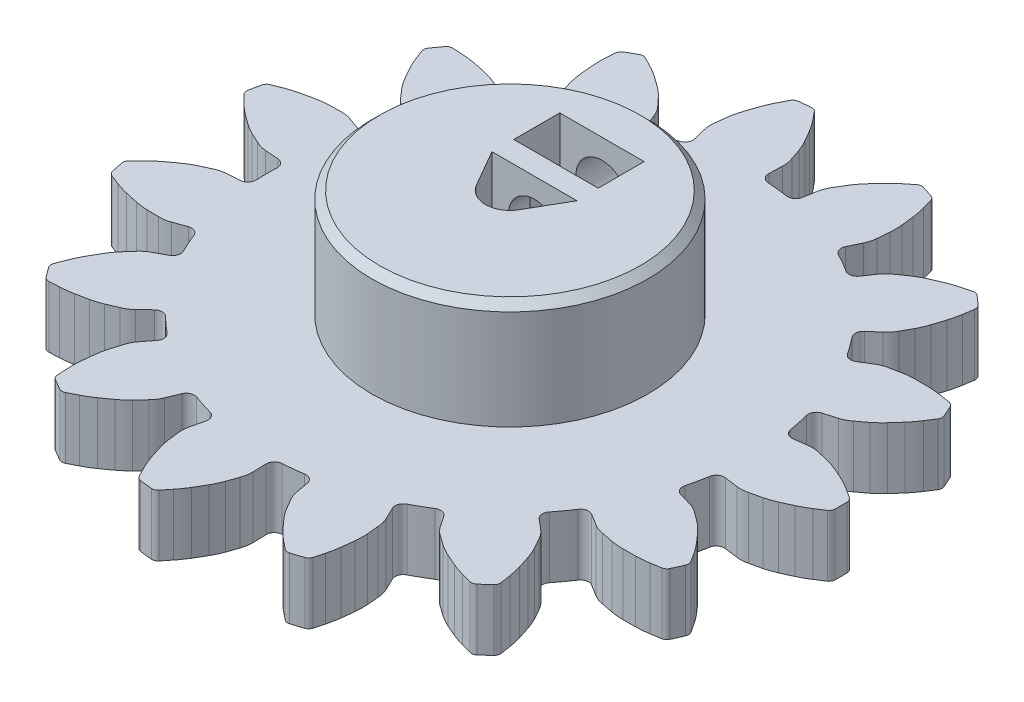
SolidWorks part; units mm, degrees
ref_plane "Front Plane" through (0, 0, 0) normal (0, 0, 1) x (1, 0, 0)
ref_plane "Top Plane" through (0, 0, 0) normal (0, 1, 0) x (1, 0, 0)
ref_plane "Right Plane" through (0, 0, 0) normal (1, 0, 0) x (0, 0, -1)
sketch "Sketch1" plane through (0, 0, 0) normal (0, 1, 0) x (1, 0, 0)
  line L0 (625.6555, 307.002) -> (626.5156, 307.1185)
  line L1 (625.6555, 302.598) -> (626.5156, 302.4815)
  line L2 (625.1464, 300.2026) -> (625.9795, 299.9593)
  line L3 (623.3551, 296.1794) -> (624.0934, 295.7232)
  line L4 (621.9157, 294.1982) -> (622.5778, 293.6371)
  line L5 (618.643, 291.2514) -> (619.1318, 290.5343)
  line L6 (616.5221, 290.027) -> (616.8987, 289.245)
  line L7 (612.3337, 288.6661) -> (612.4887, 287.8121)
  line L8 (609.8982, 288.4101) -> (609.9242, 287.5426)
  line L9 (605.5184, 288.8704) -> (605.3126, 288.0273)
  line L10 (603.1894, 289.6272) -> (602.8603, 288.8241)
  line L11 (599.3755, 291.8292) -> (598.8445, 291.1426)
  line L12 (597.5556, 293.4678) -> (596.9283, 292.868)
  line L13 (594.967, 297.0306) -> (594.2027, 296.6194)
  line L14 (593.9709, 299.2679) -> (593.1539, 298.975)
  line L15 (593.0553, 303.5755) -> (592.1898, 303.5107)
  line L16 (593.0553, 306.0245) -> (592.1898, 306.0893)
  line L17 (593.9709, 310.3321) -> (593.1539, 310.625)
  line L18 (594.967, 312.5694) -> (594.2027, 312.9806)
  line L19 (597.5556, 316.1322) -> (596.9283, 316.732)
  line L20 (599.3755, 317.7708) -> (598.8445, 318.4574)
  line L21 (603.1894, 319.9728) -> (602.8603, 320.7759)
  line L22 (605.5184, 320.7296) -> (605.3126, 321.5727)
  line L23 (609.8982, 321.1899) -> (609.9242, 322.0574)
  line L24 (612.3337, 320.9339) -> (612.4887, 321.7879)
  line L25 (616.5221, 319.573) -> (616.8987, 320.355)
  line L26 (618.643, 318.3486) -> (619.1318, 319.0657)
  line L27 (621.9157, 315.4018) -> (622.5778, 315.9629)
  line L28 (623.3551, 313.4206) -> (624.0934, 313.8768)
  line L29 (625.1464, 309.3974) -> (625.9795, 309.6407)
  line L30 (593.5318, 304.8) -> (630.9968, 304.8) construction
  line L31 (607.15, 326.2717) -> (611.0662, 289.012) construction
  arc A0 (625.0608, 307.4397) -> (624.9349, 308.1006) centre (609.4068, 304.8) ccw
  arc A1 (627.2484, 307.0745) -> (626.5156, 307.1185) centre (626.7704, 305.238) ccw
  arc A2 (627.9948, 306.9048) -> (627.2484, 307.0745) centre (97.3308, -2025.8777) ccw
  arc A3 (628.7466, 306.6443) -> (627.9948, 306.9048) centre (626.7164, 302.0004) ccw
  arc A4 (629.499, 306.3037) -> (628.7466, 306.6443) centre (616.4504, 278.4846) ccw
  arc A5 (630.2476, 305.8885) -> (629.499, 306.3037) centre (626.7956, 300.5468) ccw
  arc A6 (630.8146, 305.5178) -> (630.2476, 305.8885) centre (599.5148, 258.2574) ccw
  arc A7 (630.9968, 304.8) -> (630.9932, 305.1924) centre (609.4068, 304.8) ccw
  arc A8 (630.9932, 305.1924) -> (630.8146, 305.5178) centre (630.5943, 305.1852) ccw
  arc A9 (625.0608, 307.4397) -> (625.6555, 307.002) centre (625.5843, 307.528) ccw
  arc A10 (624.9349, 301.4994) -> (625.0608, 302.1603) centre (609.4068, 304.8) ccw
  arc A11 (626.5156, 302.4815) -> (627.2484, 302.5255) centre (626.7704, 304.362) ccw
  arc A12 (627.2484, 302.5255) -> (627.9948, 302.6952) centre (97.3308, 2635.4777) ccw
  arc A13 (627.9948, 302.6952) -> (628.7466, 302.9557) centre (626.7164, 307.5996) ccw
  arc A14 (628.7466, 302.9557) -> (629.499, 303.2963) centre (616.4504, 331.1154) ccw
  arc A15 (629.499, 303.2963) -> (630.2476, 303.7115) centre (626.7956, 309.0532) ccw
  arc A16 (630.2476, 303.7115) -> (630.8146, 304.0822) centre (599.5148, 351.3426) ccw
  arc A17 (630.9932, 304.4076) -> (630.9968, 304.8) centre (609.4068, 304.8) ccw
  arc A18 (630.8146, 304.0822) -> (630.9932, 304.4076) centre (630.5943, 304.4148) ccw
  arc A19 (625.6555, 302.598) -> (625.0608, 302.1603) centre (625.5843, 302.072) ccw
  arc A20 (624.7811, 300.8445) -> (624.9349, 301.4994) centre (609.4068, 304.8) ccw
  arc A21 (626.631, 299.621) -> (625.9795, 299.9593) centre (625.4473, 298.1377) ccw
  arc A22 (627.2439, 299.1624) -> (626.631, 299.621) centre (-806.37, -1616.1) ccw
  arc A23 (627.8248, 298.6186) -> (627.2439, 299.1624) centre (624.0812, 295.202) ccw
  arc A24 (628.3735, 298.0014) -> (627.8248, 298.6186) centre (605.138, 277.8948) ccw
  arc A25 (628.8885, 297.3177) -> (628.3735, 298.0014) centre (623.5623, 293.8419) ccw
  arc A26 (629.2558, 296.7484) -> (628.8885, 297.3177) centre (581.4394, 266.3046) ccw
  arc A27 (629.1302, 296.0186) -> (629.2866, 296.3785) centre (609.4068, 304.8) ccw
  arc A28 (629.2866, 296.3785) -> (629.2558, 296.7484) centre (628.9192, 296.5341) ccw
  arc A29 (624.7811, 300.8445) -> (625.1464, 300.2026) centre (625.2952, 300.7122) ccw
  arc A30 (622.2499, 295.4689) -> (622.6337, 296.0214) centre (609.4068, 304.8) ccw
  arc A31 (624.0934, 295.7232) -> (624.7808, 295.4653) centre (625.0911, 297.3375) ccw
  arc A32 (624.7808, 295.4653) -> (625.5316, 295.3167) centre (1089.5741, 2642.2601) ccw
  arc A33 (625.5316, 295.3167) -> (626.3245, 295.2489) centre (626.3586, 300.3171) ccw
  arc A34 (626.3245, 295.2489) -> (627.1503, 295.2541) centre (626.5449, 325.9754) ccw
  arc A35 (627.1503, 295.2541) -> (628.0031, 295.3289) centre (627.0222, 301.6128) ccw
  arc A36 (628.0031, 295.3289) -> (628.6718, 295.4369) centre (619.3006, 351.3423) ccw
  arc A37 (628.9674, 295.6615) -> (629.1302, 296.0186) centre (609.4068, 304.8) ccw
  arc A38 (628.6718, 295.4369) -> (628.9674, 295.6615) centre (628.6059, 295.8304) ccw
  arc A39 (623.3551, 296.1794) -> (622.6337, 296.0214) centre (623.0761, 295.7279) ccw
  arc A40 (621.8431, 294.9331) -> (622.2499, 295.4689) centre (609.4068, 304.8) ccw
  arc A41 (623.0354, 293.0631) -> (622.5778, 293.6371) centre (621.3508, 292.1894) ccw
  arc A42 (623.4088, 292.3948) -> (623.0354, 293.0631) centre (-1465.27, -874.1812) ccw
  arc A43 (623.7183, 291.6618) -> (623.4088, 292.3948) centre (618.9087, 290.0631) ccw
  arc A44 (623.9685, 290.8747) -> (623.7183, 291.6618) centre (594.5637, 281.9572) ccw
  arc A45 (624.1609, 290.0406) -> (623.9685, 290.8747) centre (617.8814, 289.0317) ccw
  arc A46 (624.2649, 289.3712) -> (624.1609, 290.0406) centre (568.1998, 281.0081) ccw
  arc A47 (623.8533, 288.7555) -> (624.1426, 289.0207) centre (609.4068, 304.8) ccw
  arc A48 (624.1426, 289.0207) -> (624.2649, 289.3712) centre (623.8702, 289.3123) ccw
  arc A49 (621.8431, 294.9331) -> (621.9157, 294.1982) centre (622.2589, 294.6032) ccw
  arc A50 (617.3443, 291.0518) -> (617.9196, 291.4005) centre (609.4068, 304.8) ccw
  arc A51 (619.1318, 290.5343) -> (619.6548, 290.0192) centre (620.6998, 291.6033) ccw
  arc A52 (619.6548, 290.0192) -> (620.2804, 289.578) centre (1998.7922, 2244.8744) ccw
  arc A53 (620.2804, 289.578) -> (620.9771, 289.1936) centre (623.0697, 293.8098) ccw
  arc A54 (620.9771, 289.1936) -> (621.7337, 288.8624) centre (633.676, 317.174) ccw
  arc A55 (621.7337, 288.8624) -> (622.5431, 288.5839) centre (624.2029, 294.7236) ccw
  arc A56 (622.5431, 288.5839) -> (623.198, 288.4106) centre (637.3756, 343.2943) ccw
  arc A57 (623.5593, 288.4956) -> (623.8533, 288.7555) centre (609.4068, 304.8) ccw
  arc A58 (623.198, 288.4106) -> (623.5593, 288.4956) centre (623.2978, 288.7969) ccw
  arc A59 (618.643, 291.2514) -> (617.9196, 291.4005) centre (618.2043, 290.9524) ccw
  arc A60 (616.7547, 290.7279) -> (617.3443, 291.0518) centre (609.4068, 304.8) ccw
  arc A61 (617.0833, 288.5345) -> (616.8987, 289.245) centre (615.189, 288.4216) ccw
  arc A62 (617.1526, 287.7722) -> (617.0833, 288.5345) centre (-1765.4397, 71.5942) ccw
  arc A63 (617.1372, 286.9766) -> (617.1526, 287.7722) centre (612.0932, 287.4725) ccw
  arc A64 (617.0457, 286.1558) -> (617.1372, 286.9766) centre (586.556, 289.9693) ccw
  arc A65 (616.8822, 285.3156) -> (617.0457, 286.1558) centre (610.7352, 286.948) ccw
  arc A66 (616.7049, 284.6618) -> (616.8822, 285.3156) centre (562.0853, 299.8254) ccw
  arc A67 (616.0785, 284.2667) -> (616.4506, 284.3913) centre (609.4068, 304.8) ccw
  arc A68 (616.4506, 284.3913) -> (616.7049, 284.6618) centre (616.3204, 284.7685) ccw
  arc A69 (616.7547, 290.7279) -> (616.5221, 290.027) centre (617.0004, 290.2573) ccw
  arc A70 (611.0662, 289.012) -> (611.7336, 289.0964) centre (609.4068, 304.8) ccw
  arc A71 (612.4887, 287.8121) -> (612.757, 287.1288) centre (614.3559, 288.1509) ccw
  arc A72 (612.757, 287.1288) -> (613.149, 286.4713) centre (2667.7729, 1512.0322) ccw
  arc A73 (613.149, 286.4713) -> (613.6291, 285.8368) centre (617.4184, 289.2027) ccw
  arc A74 (613.6291, 285.8368) -> (614.1855, 285.2265) centre (636.6108, 306.2331) ccw
  arc A75 (614.1855, 285.2265) -> (614.8117, 284.6429) centre (618.8253, 289.5766) ccw
  arc A76 (614.8117, 284.6429) -> (615.3395, 284.2181) centre (650.6147, 328.5903) ccw
  arc A77 (615.7042, 284.1488) -> (616.0785, 284.2667) centre (609.4068, 304.8) ccw
  arc A78 (615.3395, 284.2181) -> (615.7042, 284.1488) centre (615.5878, 284.5305) ccw
  arc A79 (612.3337, 288.6661) -> (611.7336, 289.0964) centre (611.8114, 288.5713) ccw
  arc A80 (610.3958, 288.9558) -> (611.0662, 289.012) centre (609.4068, 304.8) ccw
  arc A81 (609.8039, 286.8184) -> (609.9242, 287.5426) centre (608.0274, 287.4858) ccw
  arc A82 (609.5571, 286.0938) -> (609.8039, 286.8184) centre (-1654.9767, 1057.693) ccw
  arc A83 (609.2194, 285.3733) -> (609.5571, 286.0938) centre (604.8132, 287.8779) ccw
  arc A84 (608.802, 284.6607) -> (609.2194, 285.3733) centre (582.4993, 300.5457) ccw
  arc A85 (608.3109, 283.9596) -> (608.802, 284.6607) centre (603.3593, 287.951) ccw
  arc A86 (607.8829, 283.4344) -> (608.3109, 283.9596) centre (564.1531, 319.5029) ccw
  arc A87 (607.15, 283.3283) -> (607.5407, 283.2908) centre (609.4068, 304.8) ccw
  arc A88 (607.5407, 283.2908) -> (607.8829, 283.4344) centre (607.5752, 283.6883) ccw
  arc A89 (610.3958, 288.9558) -> (609.8982, 288.4101) centre (610.4289, 288.426) ccw
  arc A90 (604.5011, 289.702) -> (605.1452, 289.5077) centre (609.4068, 304.8) ccw
  arc A91 (605.3126, 288.0273) -> (605.2798, 287.2939) centre (607.1562, 287.5773) ccw
  arc A92 (605.2798, 287.2939) -> (605.3705, 286.5339) centre (2980.8434, 570.4486) ccw
  arc A93 (605.3705, 286.5339) -> (605.551, 285.7589) centre (610.3817, 287.2926) ccw
  arc A94 (605.551, 285.7589) -> (605.8111, 284.975) centre (634.8418, 295.0443) ccw
  arc A95 (605.8111, 284.975) -> (606.1458, 284.1872) centre (611.8191, 287.0619) ccw
  arc A96 (606.1458, 284.1872) -> (606.4552, 283.5845) centre (656.7285, 309.7728) ccw
  arc A97 (606.7601, 283.3728) -> (607.15, 283.3283) centre (609.4068, 304.8) ccw
  arc A98 (606.4552, 283.5845) -> (606.7601, 283.3728) centre (606.809, 283.7688) ccw
  arc A99 (605.5184, 288.8704) -> (605.1452, 289.5077) centre (605.0027, 288.9963) ccw
  arc A100 (603.8659, 289.9234) -> (604.5011, 289.702) centre (609.4068, 304.8) ccw
  arc A101 (602.4558, 288.2115) -> (602.8603, 288.8241) centre (601.1043, 289.5437) ccw
  arc A102 (601.9356, 287.6499) -> (602.4558, 288.2115) centre (-1152.9813, 1913.6097) ccw
  arc A103 (601.3341, 287.1291) -> (601.9356, 287.6499) centre (598.3274, 291.2093) ccw
  arc A104 (600.6629, 286.6478) -> (601.3341, 287.1291) centre (583.0952, 311.8578) ccw
  arc A105 (599.9291, 286.2071) -> (600.6629, 286.6478) centre (597.029, 291.8675) ccw
  arc A106 (599.3245, 285.9014) -> (599.9291, 286.2071) centre (574.0457, 336.6381) ccw
  arc A107 (598.6118, 286.1025) -> (598.9534, 285.9094) centre (609.4068, 304.8) ccw
  arc A108 (598.9534, 285.9094) -> (599.3245, 285.9014) centre (599.1466, 286.2585) ccw
  arc A109 (603.8659, 289.9234) -> (603.1894, 289.6272) centre (603.6806, 289.4259) ccw
  arc A110 (598.7843, 293.0026) -> (599.2937, 292.5631) centre (609.4068, 304.8) ccw
  arc A111 (598.8445, 291.1426) -> (598.5162, 290.486) centre (600.3457, 289.9817) ccw
  arc A112 (598.5162, 290.486) -> (598.29, 289.7548) centre (2883.8709, -417.068) ccw
  arc A113 (598.29, 289.7548) -> (598.1397, 288.9734) centre (603.1765, 288.4096) ccw
  arc A114 (598.1397, 288.9734) -> (598.0585, 288.1515) centre (628.6748, 285.5424) ccw
  arc A115 (598.0585, 288.1515) -> (598.0437, 287.2956) centre (604.3958, 287.6143) ccw
  arc A116 (598.0437, 287.2956) -> (598.0812, 286.6192) centre (654.6599, 290.0954) ccw
  arc A117 (598.2737, 286.3018) -> (598.6118, 286.1025) centre (609.4068, 304.8) ccw
  arc A118 (598.0812, 286.6192) -> (598.2737, 286.3018) centre (598.4795, 286.6437) ccw
  arc A119 (599.3755, 291.8292) -> (599.2937, 292.5631) centre (598.9555, 292.1539) ccw
  arc A120 (598.294, 293.4632) -> (598.7843, 293.0026) centre (609.4068, 304.8) ccw
  arc A121 (596.3096, 292.4729) -> (596.9283, 292.868) centre (595.6168, 294.2396) ccw
  arc A122 (595.606, 292.1714) -> (596.3096, 292.4729) centre (-346.253, 2491.3486) ccw
  arc A123 (594.8446, 291.9402) -> (595.606, 292.1714) centre (593.7574, 296.8906) ccw
  arc A124 (594.0357, 291.7736) -> (594.8446, 291.9402) centre (588.2406, 321.9495) ccw
  arc A125 (593.186, 291.6695) -> (594.0357, 291.7736) centre (592.839, 298.02) ccw
  arc A126 (592.5094, 291.6361) -> (593.186, 291.6695) centre (590.0525, 348.2682) ccw
  arc A127 (591.9401, 292.1097) -> (592.1737, 291.7943) centre (609.4068, 304.8) ccw
  arc A128 (592.1737, 291.7943) -> (592.5094, 291.6361) centre (592.4921, 292.0347) ccw
  arc A129 (598.294, 293.4632) -> (597.5556, 293.4678) centre (597.9224, 293.0841) ccw
  arc A130 (594.9043, 298.3431) -> (595.1908, 297.7344) centre (609.4068, 304.8) ccw
  arc A131 (594.2027, 296.6194) -> (593.6357, 296.1531) centre (595.1019, 294.9483) ccw
  arc A132 (593.6357, 296.1531) -> (593.1316, 295.5771) centre (2393.623, -1279.7672) ccw
  arc A133 (593.1316, 295.5771) -> (592.6765, 294.9244) centre (597.0486, 292.3607) ccw
  arc A134 (592.6765, 294.9244) -> (592.268, 294.2066) centre (619.1762, 279.3703) ccw
  arc A135 (592.268, 294.2066) -> (591.9064, 293.4307) centre (597.8389, 291.1382) ccw
  arc A136 (591.9064, 293.4307) -> (591.6656, 292.7975) centre (644.7667, 272.9606) ccw
  arc A137 (591.7123, 292.4293) -> (591.9401, 292.1097) centre (609.4068, 304.8) ccw
  arc A138 (591.6656, 292.7975) -> (591.7123, 292.4293) centre (592.0393, 292.6579) ccw
  arc A139 (594.967, 297.0306) -> (595.1908, 297.7344) centre (594.7155, 297.4981) ccw
  arc A140 (594.6437, 298.9633) -> (594.9043, 298.3431) centre (609.4068, 304.8) ccw
  arc A141 (592.428, 298.8657) -> (593.1539, 298.975) centre (592.5137, 300.7615) ccw
  arc A142 (591.6626, 298.8765) -> (592.428, 298.8657) centre (625.7176, 2691.0134) ccw
  arc A143 (590.873, 298.975) -> (591.6626, 298.8765) centre (591.8934, 303.9396) ccw
  arc A144 (590.0663, 299.1518) -> (590.873, 298.975) centre (597.0459, 329.0759) ccw
  arc A145 (589.2477, 299.4022) -> (590.0663, 299.1518) centre (591.5137, 305.3449) ccw
  arc A146 (588.616, 299.6469) -> (589.2477, 299.4022) centre (609.4059, 352.3822) ccw
  arc A147 (588.2886, 300.3112) -> (588.3737, 299.9281) centre (609.4068, 304.8) ccw
  arc A148 (588.3737, 299.9281) -> (588.616, 299.6469) centre (588.7624, 300.0181) ccw
  arc A149 (594.6437, 298.9633) -> (593.9709, 299.2679) centre (594.15, 298.7681) ccw
  arc A150 (593.5318, 304.8) -> (593.546, 304.1274) centre (609.4068, 304.8) ccw
  arc A151 (592.1898, 303.5107) -> (591.4822, 303.3153) centre (592.3316, 301.6183) ccw
  arc A152 (591.4822, 303.3153) -> (590.7874, 302.9942) centre (1594.8679, -1868.4803) ccw
  arc A153 (590.7874, 302.9942) -> (590.1061, 302.583) centre (593.0575, 298.4627) ccw
  arc A154 (590.1061, 302.583) -> (589.441, 302.0934) centre (607.9884, 277.5952) ccw
  arc A155 (589.441, 302.0934) -> (588.7951, 301.5317) centre (593.2823, 297.0244) ccw
  arc A156 (588.7951, 301.5317) -> (588.3175, 301.0512) centre (628.7594, 261.3311) ccw
  arc A157 (588.2105, 300.6958) -> (588.2886, 300.3112) centre (609.4068, 304.8) ccw
  arc A158 (588.3175, 301.0512) -> (588.2105, 300.6958) centre (588.6022, 300.7716) ccw
  arc A159 (593.0553, 303.5755) -> (593.546, 304.1274) centre (593.0157, 304.1049) ccw
  arc A160 (593.546, 305.4726) -> (593.5318, 304.8) centre (609.4068, 304.8) ccw
  arc A161 (591.4822, 306.2847) -> (592.1898, 306.0893) centre (592.3316, 307.9817) ccw
  arc A162 (590.7874, 306.6058) -> (591.4822, 306.2847) centre (1594.8679, 2478.0803) ccw
  arc A163 (590.1061, 307.017) -> (590.7874, 306.6058) centre (593.0575, 311.1373) ccw
  arc A164 (589.441, 307.5066) -> (590.1061, 307.017) centre (607.9884, 332.0048) ccw
  arc A165 (588.7951, 308.0683) -> (589.441, 307.5066) centre (593.2823, 312.5756) ccw
  arc A166 (588.3175, 308.5488) -> (588.7951, 308.0683) centre (628.7594, 348.2689) ccw
  arc A167 (588.2886, 309.2888) -> (588.2105, 308.9042) centre (609.4068, 304.8) ccw
  arc A168 (588.2105, 308.9042) -> (588.3175, 308.5488) centre (588.6022, 308.8284) ccw
  arc A169 (593.546, 305.4726) -> (593.0553, 306.0245) centre (593.0157, 305.4951) ccw
  arc A170 (594.9043, 311.2569) -> (594.6437, 310.6367) centre (609.4068, 304.8) ccw
  arc A171 (593.1539, 310.625) -> (592.428, 310.7343) centre (592.5137, 308.8385) ccw
  arc A172 (592.428, 310.7343) -> (591.6626, 310.7235) centre (625.7176, -2081.4134) ccw
  arc A173 (591.6626, 310.7235) -> (590.873, 310.625) centre (591.8934, 305.6604) ccw
  arc A174 (590.873, 310.625) -> (590.0663, 310.4482) centre (597.0459, 280.5241) ccw
  arc A175 (590.0663, 310.4482) -> (589.2477, 310.1978) centre (591.5137, 304.2551) ccw
  arc A176 (589.2477, 310.1978) -> (588.616, 309.9531) centre (609.4059, 257.2178) ccw
  arc A177 (588.3737, 309.6719) -> (588.2886, 309.2888) centre (609.4068, 304.8) ccw
  arc A178 (588.616, 309.9531) -> (588.3737, 309.6719) centre (588.7624, 309.5819) ccw
  arc A179 (593.9709, 310.3321) -> (594.6437, 310.6367) centre (594.15, 310.8319) ccw
  arc A180 (595.1908, 311.8656) -> (594.9043, 311.2569) centre (609.4068, 304.8) ccw
  arc A181 (593.6357, 313.4469) -> (594.2027, 312.9806) centre (595.1019, 314.6517) ccw
  arc A182 (593.1316, 314.0229) -> (593.6357, 313.4469) centre (2393.623, 1889.3672) ccw
  arc A183 (592.6765, 314.6756) -> (593.1316, 314.0229) centre (597.0486, 317.2393) ccw
  arc A184 (592.268, 315.3934) -> (592.6765, 314.6756) centre (619.1762, 330.2297) ccw
  arc A185 (591.9064, 316.1693) -> (592.268, 315.3934) centre (597.8389, 318.4618) ccw
  arc A186 (591.6656, 316.8025) -> (591.9064, 316.1693) centre (644.7667, 336.6394) ccw
  arc A187 (591.9401, 317.4903) -> (591.7123, 317.1707) centre (609.4068, 304.8) ccw
  arc A188 (591.7123, 317.1707) -> (591.6656, 316.8025) centre (592.0393, 316.9421) ccw
  arc A189 (595.1908, 311.8656) -> (594.967, 312.5694) centre (594.7155, 312.1019) ccw
  arc A190 (598.7843, 316.5974) -> (598.294, 316.1368) centre (609.4068, 304.8) ccw
  arc A191 (596.9283, 316.732) -> (596.3096, 317.1271) centre (595.6168, 315.3604) ccw
  arc A192 (596.3096, 317.1271) -> (595.606, 317.4286) centre (-346.253, -1881.7486) ccw
  arc A193 (595.606, 317.4286) -> (594.8446, 317.6598) centre (593.7574, 312.7094) ccw
  arc A194 (594.8446, 317.6598) -> (594.0357, 317.8264) centre (588.2406, 287.6505) ccw
  arc A195 (594.0357, 317.8264) -> (593.186, 317.9305) centre (592.839, 311.58) ccw
  arc A196 (593.186, 317.9305) -> (592.5094, 317.9639) centre (590.0525, 261.3318) ccw
  arc A197 (592.1737, 317.8057) -> (591.9401, 317.4903) centre (609.4068, 304.8) ccw
  arc A198 (592.5094, 317.9639) -> (592.1737, 317.8057) centre (592.4921, 317.5653) ccw
  arc A199 (597.5556, 316.1322) -> (598.294, 316.1368) centre (597.9224, 316.5159) ccw
  arc A200 (599.2937, 317.0369) -> (598.7843, 316.5974) centre (609.4068, 304.8) ccw
  arc A201 (598.5162, 319.114) -> (598.8445, 318.4574) centre (600.3457, 319.6183) ccw
  arc A202 (598.29, 319.8452) -> (598.5162, 319.114) centre (2883.8709, 1026.668) ccw
  arc A203 (598.1397, 320.6266) -> (598.29, 319.8452) centre (603.1765, 321.1904) ccw
  arc A204 (598.0585, 321.4485) -> (598.1397, 320.6266) centre (628.6748, 324.0576) ccw
  arc A205 (598.0437, 322.3044) -> (598.0585, 321.4485) centre (604.3958, 321.9857) ccw
  arc A206 (598.0812, 322.9808) -> (598.0437, 322.3044) centre (654.6599, 319.5046) ccw
  arc A207 (598.6118, 323.4975) -> (598.2737, 323.2982) centre (609.4068, 304.8) ccw
  arc A208 (598.2737, 323.2982) -> (598.0812, 322.9808) centre (598.4795, 322.9563) ccw
  arc A209 (599.2937, 317.0369) -> (599.3755, 317.7708) centre (598.9555, 317.4461) ccw
  arc A210 (604.5011, 319.898) -> (603.8659, 319.6766) centre (609.4068, 304.8) ccw
  arc A211 (602.8603, 320.7759) -> (602.4558, 321.3885) centre (601.1043, 320.0563) ccw
  arc A212 (602.4558, 321.3885) -> (601.9356, 321.9501) centre (-1152.9813, -1304.0097) ccw
  arc A213 (601.9356, 321.9501) -> (601.3341, 322.4709) centre (598.3274, 318.3907) ccw
  arc A214 (601.3341, 322.4709) -> (600.6629, 322.9522) centre (583.0952, 297.7422) ccw
  arc A215 (600.6629, 322.9522) -> (599.9291, 323.3929) centre (597.029, 317.7325) ccw
  arc A216 (599.9291, 323.3929) -> (599.3245, 323.6986) centre (574.0457, 272.9619) ccw
  arc A217 (598.9534, 323.6906) -> (598.6118, 323.4975) centre (609.4068, 304.8) ccw
  arc A218 (599.3245, 323.6986) -> (598.9534, 323.6906) centre (599.1466, 323.3415) ccw
  arc A219 (603.1894, 319.9728) -> (603.8659, 319.6766) centre (603.6806, 320.1741) ccw
  arc A220 (605.1452, 320.0923) -> (604.5011, 319.898) centre (609.4068, 304.8) ccw
  arc A221 (605.2798, 322.3061) -> (605.3126, 321.5727) centre (607.1562, 322.0227) ccw
  arc A222 (605.3705, 323.0661) -> (605.2798, 322.3061) centre (2980.8434, 39.1514) ccw
  arc A223 (605.551, 323.8411) -> (605.3705, 323.0661) centre (610.3817, 322.3074) ccw
  arc A224 (605.8111, 324.625) -> (605.551, 323.8411) centre (634.8418, 314.5557) ccw
  arc A225 (606.1458, 325.4128) -> (605.8111, 324.625) centre (611.8191, 322.5381) ccw
  arc A226 (606.4552, 326.0155) -> (606.1458, 325.4128) centre (656.7285, 299.8272) ccw
  arc A227 (607.15, 326.2717) -> (606.7601, 326.2272) centre (609.4068, 304.8) ccw
  arc A228 (606.7601, 326.2272) -> (606.4552, 326.0155) centre (606.809, 325.8312) ccw
  arc A229 (605.1452, 320.0923) -> (605.5184, 320.7296) centre (605.0027, 320.6037) ccw
  arc A230 (611.0662, 320.588) -> (610.3958, 320.6442) centre (609.4068, 304.8) ccw
  arc A231 (609.9242, 322.0574) -> (609.8039, 322.7816) centre (608.0274, 322.1142) ccw
  arc A232 (609.8039, 322.7816) -> (609.5571, 323.5062) centre (-1654.9767, -448.093) ccw
  arc A233 (609.5571, 323.5062) -> (609.2194, 324.2267) centre (604.8132, 321.7221) ccw
  arc A234 (609.2194, 324.2267) -> (608.802, 324.9393) centre (582.4993, 309.0543) ccw
  arc A235 (608.802, 324.9393) -> (608.3109, 325.6404) centre (603.3593, 321.649) ccw
  arc A236 (608.3109, 325.6404) -> (607.8829, 326.1656) centre (564.1531, 290.0971) ccw
  arc A237 (607.5407, 326.3092) -> (607.15, 326.2717) centre (609.4068, 304.8) ccw
  arc A238 (607.8829, 326.1656) -> (607.5407, 326.3092) centre (607.5752, 325.9117) ccw
  arc A239 (609.8982, 321.1899) -> (610.3958, 320.6442) centre (610.4289, 321.174) ccw
  arc A240 (611.7336, 320.5036) -> (611.0662, 320.588) centre (609.4068, 304.8) ccw
  arc A241 (612.757, 322.4712) -> (612.4887, 321.7879) centre (614.3559, 321.4491) ccw
  arc A242 (613.149, 323.1287) -> (612.757, 322.4712) centre (2667.7729, -902.4322) ccw
  arc A243 (613.6291, 323.7632) -> (613.149, 323.1287) centre (617.4184, 320.3973) ccw
  arc A244 (614.1855, 324.3735) -> (613.6291, 323.7632) centre (636.6108, 303.3669) ccw
  arc A245 (614.8117, 324.9571) -> (614.1855, 324.3735) centre (618.8253, 320.0234) ccw
  arc A246 (615.3395, 325.3819) -> (614.8117, 324.9571) centre (650.6147, 281.0097) ccw
  arc A247 (616.0785, 325.3333) -> (615.7042, 325.4512) centre (609.4068, 304.8) ccw
  arc A248 (615.7042, 325.4512) -> (615.3395, 325.3819) centre (615.5878, 325.0695) ccw
  arc A249 (611.7336, 320.5036) -> (612.3337, 320.9339) centre (611.8114, 321.0287) ccw
  arc A250 (617.3443, 318.5482) -> (616.7547, 318.8721) centre (609.4068, 304.8) ccw
  arc A251 (616.8987, 320.355) -> (617.0833, 321.0655) centre (615.189, 321.1784) ccw
  arc A252 (617.0833, 321.0655) -> (617.1526, 321.8278) centre (-1765.4397, 538.0058) ccw
  arc A253 (617.1526, 321.8278) -> (617.1372, 322.6234) centre (612.0932, 322.1275) ccw
  arc A254 (617.1372, 322.6234) -> (617.0457, 323.4442) centre (586.556, 319.6307) ccw
  arc A255 (617.0457, 323.4442) -> (616.8822, 324.2844) centre (610.7352, 322.652) ccw
  arc A256 (616.8822, 324.2844) -> (616.7049, 324.9382) centre (562.0853, 309.7746) ccw
  arc A257 (616.4506, 325.2087) -> (616.0785, 325.3333) centre (609.4068, 304.8) ccw
  arc A258 (616.7049, 324.9382) -> (616.4506, 325.2087) centre (616.3204, 324.8315) ccw
  arc A259 (616.5221, 319.573) -> (616.7547, 318.8721) centre (617.0004, 319.3427) ccw
  arc A260 (617.9196, 318.1995) -> (617.3443, 318.5482) centre (609.4068, 304.8) ccw
  arc A261 (619.6548, 319.5808) -> (619.1318, 319.0657) centre (620.6998, 317.9967) ccw
  arc A262 (620.2804, 320.022) -> (619.6548, 319.5808) centre (1998.7922, -1635.2744) ccw
  arc A263 (620.9771, 320.4064) -> (620.2804, 320.022) centre (623.0697, 315.7902) ccw
  arc A264 (621.7337, 320.7376) -> (620.9771, 320.4064) centre (633.676, 292.426) ccw
  arc A265 (622.5431, 321.0161) -> (621.7337, 320.7376) centre (624.2029, 314.8764) ccw
  arc A266 (623.198, 321.1894) -> (622.5431, 321.0161) centre (637.3756, 266.3057) ccw
  arc A267 (623.8533, 320.8445) -> (623.5593, 321.1044) centre (609.4068, 304.8) ccw
  arc A268 (623.5593, 321.1044) -> (623.198, 321.1894) centre (623.2978, 320.8031) ccw
  arc A269 (617.9196, 318.1995) -> (618.643, 318.3486) centre (618.2043, 318.6476) ccw
  arc A270 (622.2499, 314.1311) -> (621.8431, 314.6669) centre (609.4068, 304.8) ccw
  arc A271 (622.5778, 315.9629) -> (623.0354, 316.5369) centre (621.3508, 317.4106) ccw
  arc A272 (623.0354, 316.5369) -> (623.4088, 317.2052) centre (-1465.27, 1483.7812) ccw
  arc A273 (623.4088, 317.2052) -> (623.7183, 317.9382) centre (618.9087, 319.5369) ccw
  arc A274 (623.7183, 317.9382) -> (623.9685, 318.7253) centre (594.5637, 327.6428) ccw
  arc A275 (623.9685, 318.7253) -> (624.1609, 319.5594) centre (617.8814, 320.5683) ccw
  arc A276 (624.1609, 319.5594) -> (624.2649, 320.2288) centre (568.1998, 328.5919) ccw
  arc A277 (624.1426, 320.5793) -> (623.8533, 320.8445) centre (609.4068, 304.8) ccw
  arc A278 (624.2649, 320.2288) -> (624.1426, 320.5793) centre (623.8702, 320.2877) ccw
  arc A279 (621.9157, 315.4018) -> (621.8431, 314.6669) centre (622.2589, 314.9968) ccw
  arc A280 (622.6337, 313.5786) -> (622.2499, 314.1311) centre (609.4068, 304.8) ccw
  arc A281 (624.7808, 314.1347) -> (624.0934, 313.8768) centre (625.0911, 312.2625) ccw
  arc A282 (625.5316, 314.2833) -> (624.7808, 314.1347) centre (1089.5741, -2032.6601) ccw
  arc A283 (626.3245, 314.3511) -> (625.5316, 314.2833) centre (626.3586, 309.2829) ccw
  arc A284 (627.1503, 314.3459) -> (626.3245, 314.3511) centre (626.5449, 283.6246) ccw
  arc A285 (628.0031, 314.2711) -> (627.1503, 314.3459) centre (627.0222, 307.9872) ccw
  arc A286 (628.6718, 314.1631) -> (628.0031, 314.2711) centre (619.3006, 258.2577) ccw
  arc A287 (629.1302, 313.5814) -> (628.9674, 313.9385) centre (609.4068, 304.8) ccw
  arc A288 (628.9674, 313.9385) -> (628.6718, 314.1631) centre (628.6059, 313.7696) ccw
  arc A289 (622.6337, 313.5786) -> (623.3551, 313.4206) centre (623.0761, 313.8721) ccw
  arc A290 (624.9349, 308.1006) -> (624.7811, 308.7555) centre (609.4068, 304.8) ccw
  arc A291 (625.9795, 309.6407) -> (626.631, 309.979) centre (625.4473, 311.4623) ccw
  arc A292 (626.631, 309.979) -> (627.2439, 310.4376) centre (-806.37, 2225.7) ccw
  arc A293 (627.2439, 310.4376) -> (627.8248, 310.9814) centre (624.0812, 314.398) ccw
  arc A294 (627.8248, 310.9814) -> (628.3735, 311.5986) centre (605.138, 331.7052) ccw
  arc A295 (628.3735, 311.5986) -> (628.8885, 312.2823) centre (623.5623, 315.7581) ccw
  arc A296 (628.8885, 312.2823) -> (629.2558, 312.8516) centre (581.4394, 343.2954) ccw
  arc A297 (629.2866, 313.2215) -> (629.1302, 313.5814) centre (609.4068, 304.8) ccw
  arc A298 (629.2558, 312.8516) -> (629.2866, 313.2215) centre (628.9192, 313.0659) ccw
  arc A299 (625.1464, 309.3974) -> (624.7811, 308.7555) centre (625.2952, 308.8878) ccw
sketch "Sketch2" plane through (0, 0, 0) normal (0, 1, 0) x (1, 0, 0)
  circle A0 centre (609.4068, 304.8) radius 9
  dimension "D1" = 18
sketch "Sketch3" plane through (0, 0, 0) normal (0, 1, 0) x (1, 0, 0)
  line L1 (612.1781, 306.4) -> (606.6355, 306.4)
  line L2 (606.6355, 306.4) -> (608.0212, 304)
  line L3 (610.7924, 304) -> (612.1781, 306.4)
  arc A0 (608.0212, 304) -> (610.7924, 304) centre (609.4068, 304.8) ccw
  dimension "D1" = 3.2
extrude "Boss-Extrude1" add sketch "Sketch1" along normal blind 4
extrude "Boss-Extrude2" add sketch "Sketch2" along normal blind 11
extrude "Cut-Extrude1" cut sketch "Sketch3" along normal through all
sketch "Sketch4" plane through (0, 11, 0) normal (0, 1, 0) x (1, 0, 0)
  line L0 (612.1781, 306.4) -> (606.6355, 306.4) construction
  line L1 (606.6568, 310.8) -> (612.1568, 310.8)
  line L2 (606.6568, 310.8) -> (606.6568, 307.8)
  line L3 (606.6568, 307.8) -> (612.1568, 307.8)
  line L4 (612.1568, 310.8) -> (612.1568, 307.8)
  line L5 (606.6568, 310.8) -> (612.1568, 307.8) construction
  line L6 (606.6568, 307.8) -> (612.1568, 310.8) construction
  circle A0 centre (609.4068, 304.8) radius 9 construction
  point P0 (609.4068, 309.3)
  point P7 (609.4068, 306.4)
  point P8 (609.4068, 304.8)
  dimension "D1" = 4.5
  dimension "D2" = 5.5
  dimension "D3" = 3
extrude "Cut-Extrude2" cut sketch "Sketch4" against normal blind 6
sketch "Sketch5" plane through (0, 0, -306.4) normal (0, 0, 1) x (1, 0, 0)
  line L0 (612.1781, 11) -> (606.6355, 11) construction
  circle A0 centre (609.4068, 8) radius 1.7
  point P4 (609.4068, 11)
  dimension "D2" = 3.4
  dimension "D1" = 3
extrude "Cut-Extrude3" cut sketch "Sketch5" against normal through all
chamfer "Chamfer1" distance 0.5 angle 45 1 edges at (609.4068, 11, -295.8)
